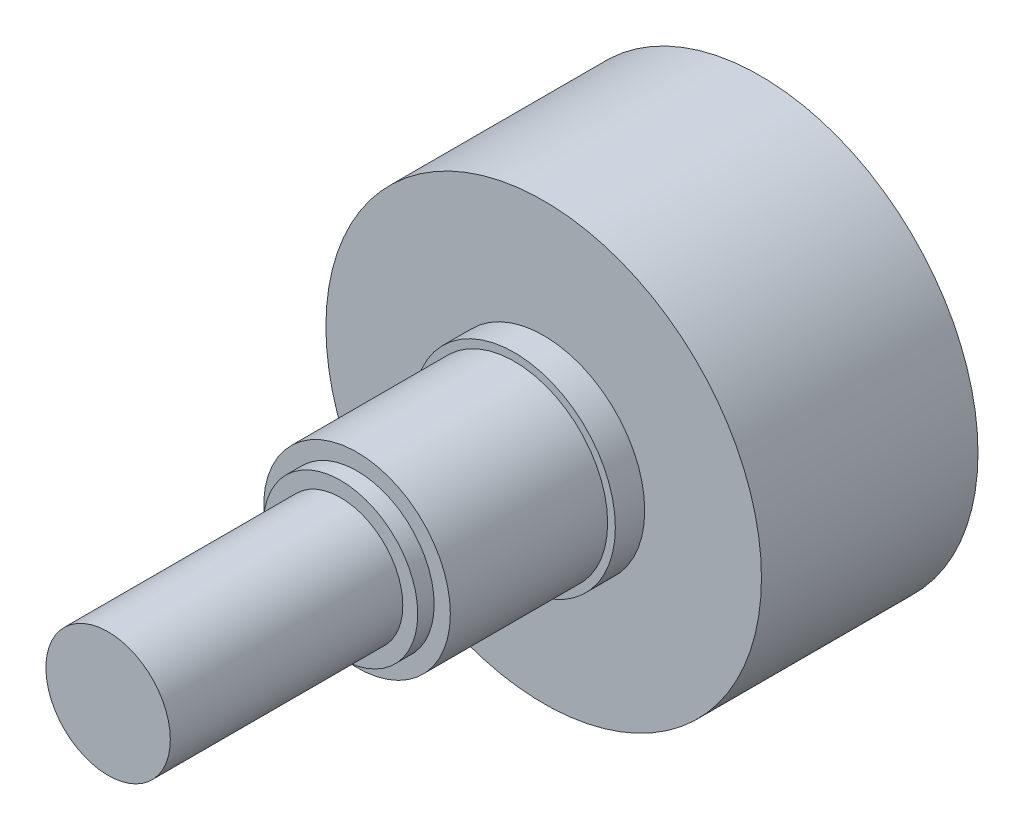
SolidWorks part; units mm, degrees
material "6061-T6 (SS)"
ref_plane "Front Plane" through (0, 0, 0) normal (0, 0, 1) x (1, 0, 0)
ref_plane "Top Plane" through (0, 0, 0) normal (0, 1, 0) x (1, 0, 0)
ref_plane "Right Plane" through (0, 0, 0) normal (1, 0, 0) x (0, 0, -1)
sketch "Sketch1" plane through (0, 0, 0) normal (0, 0, 1) x (1, 0, 0)
  circle A0 centre (0, 0) radius 11.1125
  dimension "D1" = 22.225
extrude "Boss-Extrude1" add sketch "Sketch1" along normal blind 11.049
sketch "Sketch2" plane through (0, 0, 11.049) normal (0, 0, 1) x (1, 0, 0)
  circle A0 centre (0, 0) radius 5.1562
  dimension "D1" = 10.3124
extrude "Boss-Extrude2" add sketch "Sketch2" along normal blind 1.4986
sketch "Sketch3" plane through (0, 0, 11.049) normal (0, 0, 1) x (1, 0, 0)
  circle A0 centre (0, 0) radius 4.7625
  dimension "D1" = 9.525
extrude "Boss-Extrude5" add sketch "Sketch3" along normal blind 9.525
sketch "Sketch4" plane through (0, 0, 20.574) normal (0, 0, 1) x (1, 0, 0)
  circle A0 centre (0, 0) radius 3.937
  dimension "D1" = 7.874
extrude "Boss-Extrude6" add sketch "Sketch4" along normal blind 0.8382
sketch "Sketch5" plane through (0, 0, 11.049) normal (0, 0, 1) x (1, 0, 0)
  circle A0 centre (0, 0) radius 3.175
  dimension "D1" = 6.35
extrude "Boss-Extrude7" add sketch "Sketch5" along normal blind 22.225
